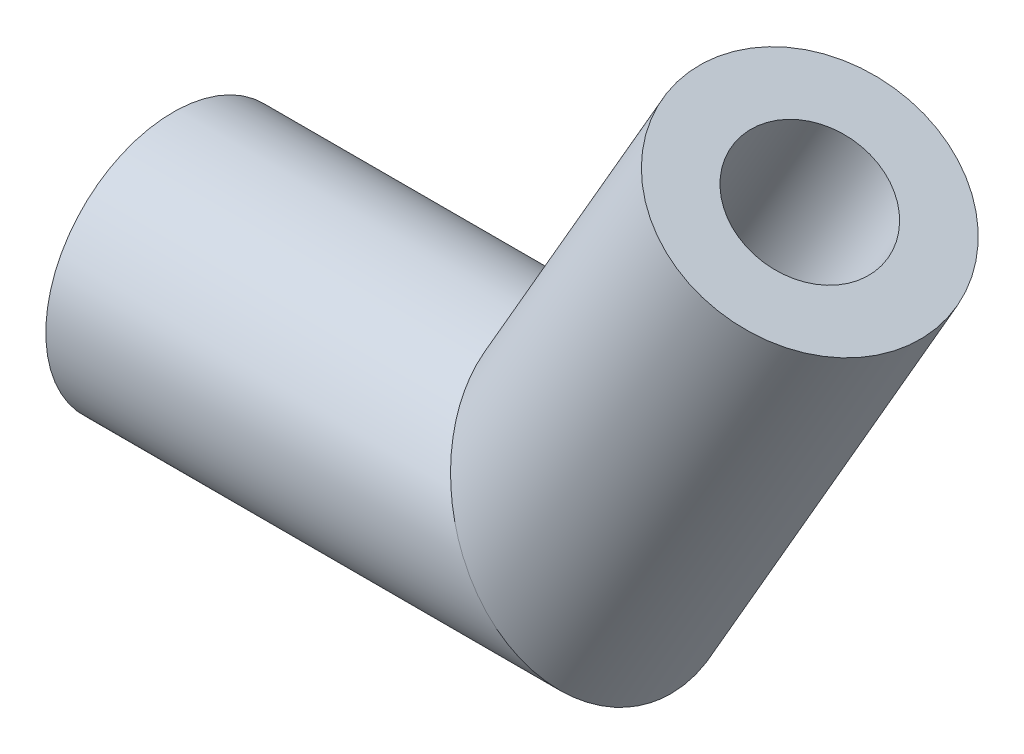
SolidWorks part; units mm, degrees
ref_plane "Front Plane" through (0, 0, 0) normal (0, 0, 1) x (1, 0, 0)
ref_plane "Top Plane" through (0, 0, 0) normal (0, 1, 0) x (1, 0, 0)
ref_plane "Right Plane" through (0, 0, 0) normal (1, 0, 0) x (0, 0, -1)
sketch "Sketch2" plane through (0, 0, 0) normal (0, 0, 1) x (1, 0, 0)
  line L0 (0, 0) -> (10, 0)
  line L1 (10, 0) -> (15, 8.6603)
  dimension "D1" = 10
  dimension "D2" = 10
  dimension "D3" = 120
sketch "Sketch3" plane through (0, 0, 0) normal (1, 0, 0) x (0, 0, -1)
  circle A0 centre (0, 0) radius 1.6
  circle A1 centre (0, 0) radius 3
  dimension "D1" = 3.2
  dimension "D2" = 6
sweep "Sweep1" add profiles "Sketch3" path "Sketch2"
